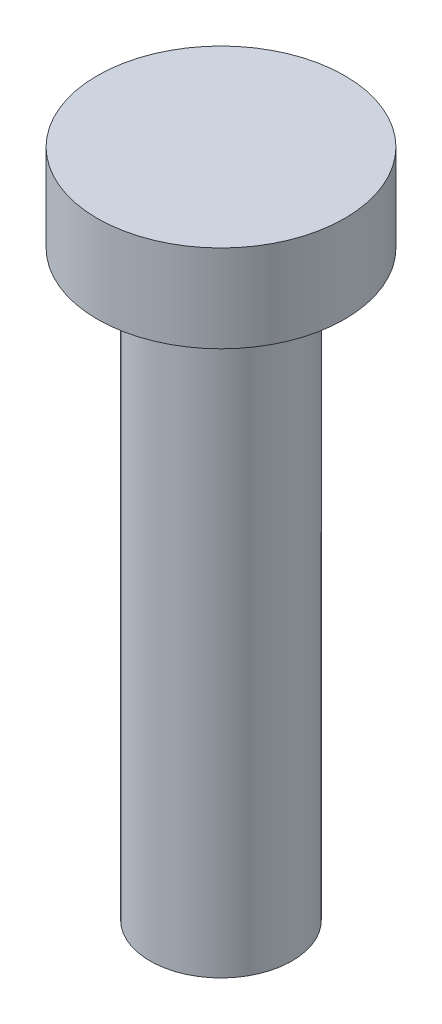
SolidWorks part; units mm, degrees
ref_plane "Front Plane" through (0, 0, 0) normal (0, 0, 1) x (1, 0, 0)
ref_plane "Top Plane" through (0, 0, 0) normal (0, 1, 0) x (1, 0, 0)
ref_plane "Right Plane" through (0, 0, 0) normal (1, 0, 0) x (0, 0, -1)
sketch "Sketch1" plane through (0, 0, 0) normal (0, 1, 0) x (1, 0, 0)
  circle A0 centre (0, 0) radius 4.25
  dimension "D1" = 8.5
extrude "Boss-Extrude1" add sketch "Sketch1" along normal blind 3
sketch "Sketch2" plane through (0, 0, 0) normal (0, -1, 0) x (1, 0, 0)
  circle A0 centre (0, 0) radius 2.44
  dimension "D1" = 4.88
extrude "Boss-Extrude2" add sketch "Sketch2" along normal blind 20
